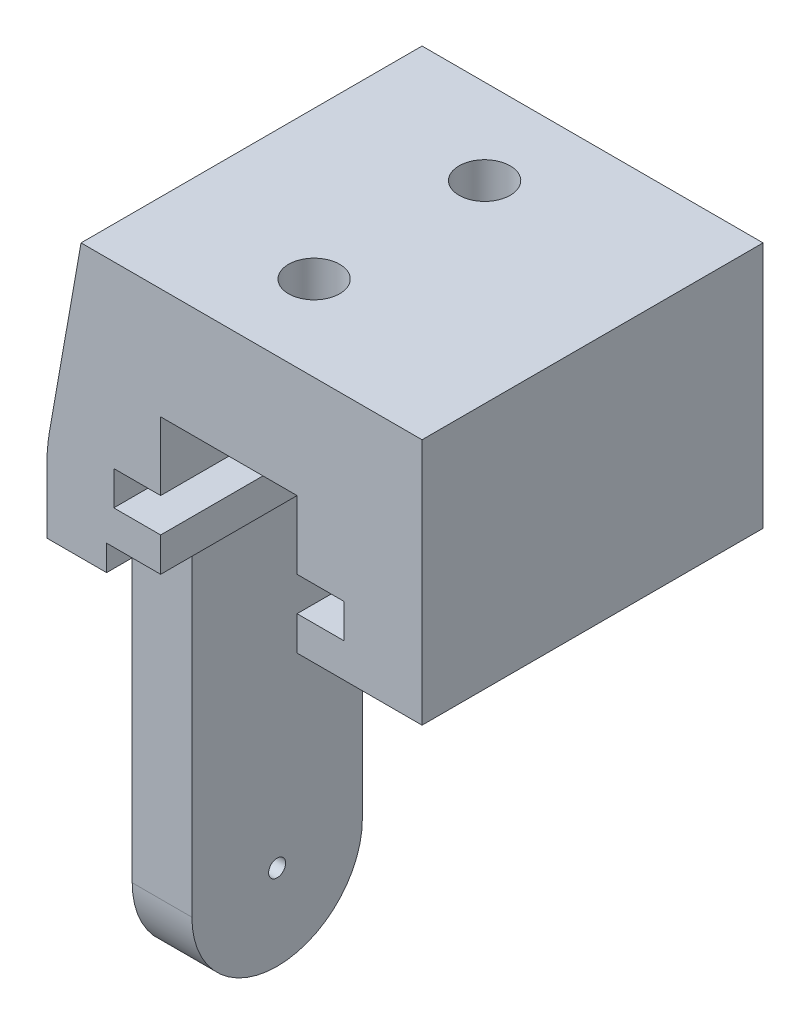
SolidWorks part; units mm, degrees
ref_plane "Front Plane" through (0, 0, 0) normal (0, 0, 1) x (1, 0, 0)
ref_plane "Top Plane" through (0, 0, 0) normal (0, 1, 0) x (1, 0, 0)
ref_plane "Right Plane" through (0, 0, 0) normal (1, 0, 0) x (0, 0, -1)
sketch "Sketch1" plane through (0, 0, 0) normal (0, 0, 1) x (1, 0, 0)
  line L1 (0, 0) -> (22, 0)
  line L2 (0, 0) -> (0, -16)
  line L3 (0, -16) -> (22, -16)
  line L4 (22, 0) -> (22, -16)
  dimension "D1" = 22
  dimension "D2" = 16
extrude "Boss-Extrude1" add sketch "Sketch1" along normal blind 20
chamfer "Chamfer1" distance 2 angle 80 1 edges at (0, 0, 10)
sketch "Sketch2" plane through (0, 0, 20) normal (0, 0, 1) x (1, 0, 0)
  line L0 (3.5, -16) -> (3.5, -14.5)
  line L1 (0, -16) -> (22, -16) construction
  line L2 (3.5, -14.5) -> (6.67, -14.5)
  line L3 (6.67, -14.5) -> (6.67, -12.5)
  line L4 (6.67, -12.5) -> (3.92, -12.5)
  line L5 (3.92, -12.5) -> (3.92, -10.5)
  line L6 (3.92, -10.5) -> (6.67, -10.5)
  line L7 (6.67, -10.5) -> (6.67, -6.5)
  line L8 (6.67, -6.5) -> (14.67, -6.5)
  line L9 (14.67, -6.5) -> (14.67, -10.5)
  line L10 (14.67, -10.5) -> (17.42, -10.5)
  line L11 (17.42, -10.5) -> (17.42, -12.5)
  line L12 (17.42, -12.5) -> (14.67, -12.5)
  line L13 (14.67, -12.5) -> (14.67, -14.5)
  line L14 (14.67, -14.5) -> (22, -14.5)
  line L15 (22, -16) -> (22, 0) construction
  line L16 (22, -14.5) -> (22, -16)
  line L17 (22, -16) -> (3.5, -16)
  dimension "D1" = 3.5
  dimension "D2" = 1.5
  dimension "D3" = 2
  dimension "D4" = 2.75
  dimension "D5" = 2
  dimension "D6" = 4
  dimension "D7" = 8
  dimension "D8" = 3.17
extrude "Cut-Extrude1" cut sketch "Sketch2" against normal up to surface (20 mm away) contours L8 L9 L10 L11 L12 L13 L14 L16 L17 L0 L2 L3 L4 L5 L6 L7 up to face at (9.2, -8.6685, 0)
fillet "Fillet1" radius 10 1 edges at (0, -11.3426, 10)
sketch "Sketch3" plane through (0, -16, 0) normal (0, -1, 0) x (1, 0, 0)
  line L0 (0, 20) -> (0, 0) construction
  line L1 (0, 15) -> (3.5, 15)
  line L2 (0, 15) -> (0, 5)
  line L3 (0, 5) -> (3.5, 5)
  line L4 (3.5, 15) -> (3.5, 5)
  line L5 (3.5, 0) -> (3.5, 20) construction
  line L6 (0, 20) -> (3.5, 20) construction
  dimension "D1" = 5
  dimension "D2" = 10
extrude "Boss-Extrude2" add sketch "Sketch3" along normal blind 20
fillet "Fillet2" radius 1 2 edges
ref_plane "Plane1" through (0, 0, 0) normal (-1, 0, 0) x (0, 0, 1)
sketch "Sketch7" plane through (0, 0, 0) normal (-1, 0, 0) x (0, 0, 1)
  line L0 (15, -36) -> (5, -36) construction
  line L1 (15, -36) -> (5, -36)
  arc A0 (15, -36) -> (5, -36) centre (10, -36) cw
extrude "Boss-Extrude3" add sketch "Sketch7" against normal up to surface (3.5 mm away) up to face at (3.5, -21.7586, 9.6)
sketch "Sketch8" plane through (0, 0, 0) normal (-1, 0, 0) x (0, 0, 1)
  circle A0 centre (10, -36) radius 0.5
  dimension "D1" = 1
extrude "Cut-Extrude2" cut sketch "Sketch8" against normal up to surface (3.5 mm away) up to face at (3.5, -22.2586, 9.6)
sketch "Sketch9" plane through (0, -6.5, 0) normal (0, -1, 0) x (1, 0, 0)
  line L0 (10.67, 20) -> (10.67, 0) construction
  line L1 (6.67, 20) -> (14.67, 20) construction
  line L2 (14.67, 0) -> (6.67, 0) construction
  circle A0 centre (10.67, 15) radius 1.5
  circle A1 centre (10.67, 5) radius 1.5
  dimension "D1" = 3
  dimension "D2" = 5
  dimension "D3" = 5
extrude "Cut-Extrude3" cut sketch "Sketch9" against normal up to surface (6.5 mm away) up to face at (12, 0, 10)
